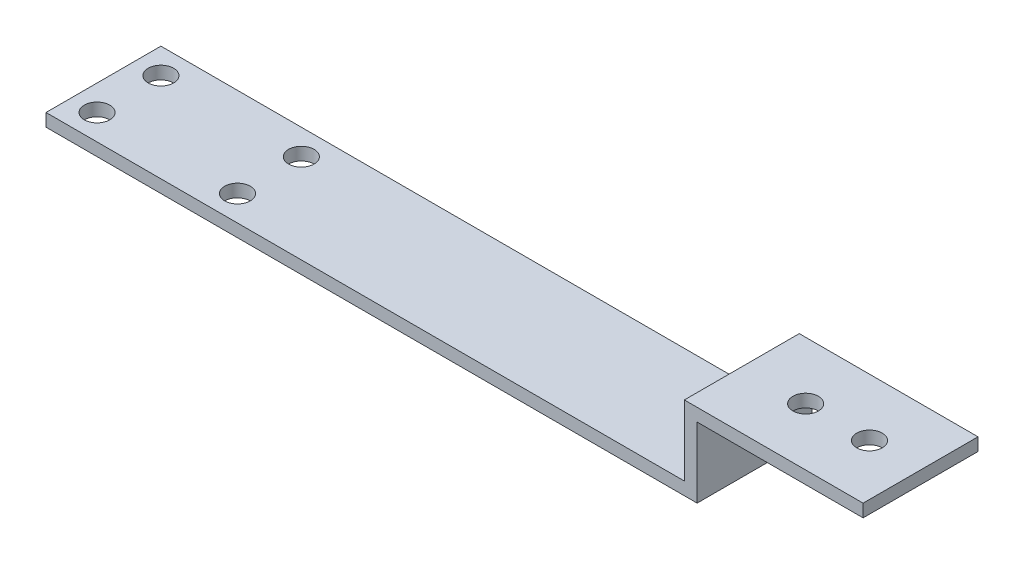
SolidWorks part; units mm, degrees
material "7075-T6 (SN)"
ref_plane "Front Plane" through (0, 0, 0) normal (0, 0, 1) x (1, 0, 0)
ref_plane "Top Plane" through (0, 0, 0) normal (0, 1, 0) x (1, 0, 0)
ref_plane "Right Plane" through (0, 0, 0) normal (1, 0, 0) x (0, 0, -1)
sketch "Sketch1" plane through (0, 0, 0) normal (0, 0, 1) x (1, 0, 0)
  line L0 (0, 0) -> (100, 0)
  line L1 (100, 0) -> (100, 11)
  line L2 (100, 11) -> (128, 11)
  line L3 (128, 11) -> (128, 9)
  line L4 (128, 9) -> (102, 9)
  line L5 (102, 9) -> (102, -2)
  line L6 (102, -2) -> (0, -2)
  line L7 (0, -2) -> (0, 0)
  dimension "D1" = 100
  dimension "D2" = 11
  dimension "D3" = 28
  dimension "D4" = 2
  dimension "D5" = 2
  dimension "D6" = 2
extrude "Boss-Extrude1" add sketch "Sketch1" along normal blind 18
sketch "Sketch2" plane through (0, 0, 0) normal (0, 1, 0) x (1, 0, 0)
  line L0 (4, 7.6163) -> (4, -29.4788) construction
  line L1 (-7.5026, -4) -> (30.9141, -4) construction
  line L2 (-7.5026, -14) -> (30.9141, -14) construction
  line L3 (0, -18) -> (0, 0) construction
  line L4 (100, -18) -> (0, -18) construction
  line L5 (100, 0) -> (0, 0) construction
  line L6 (26, 9.2017) -> (26, -29.4788) construction
  circle A0 centre (4, -14) radius 2
  circle A1 centre (4, -4) radius 2
  circle A2 centre (26, -14) radius 2
  circle A3 centre (26, -4) radius 2
  dimension "D4" = 4
  dimension "D5" = 4
  dimension "D7" = 4
  dimension "D8" = 4
  dimension "D1" = 4
  dimension "D2" = 4
  dimension "D3" = 4
  dimension "D6" = 26
extrude "Cut-Extrude1" cut sketch "Sketch2" against normal up to next
sketch "Sketch3" plane through (0, 9, 0) normal (0, -1, 0) x (1, 0, 0)
  line L0 (132.4314, 9) -> (94.1527, 9) construction
  line L1 (128, 18) -> (128, 0) construction
  line L3 (102, 18) -> (102, 0) construction
  circle A0 centre (120, 9) radius 2
  circle A1 centre (110, 9) radius 2
  point P4 (128, 9)
  dimension "D1" = 8
  dimension "D2" = 8
  dimension "D3" = 4
  dimension "D4" = 4
extrude "Cut-Extrude2" cut sketch "Sketch3" against normal up to next
